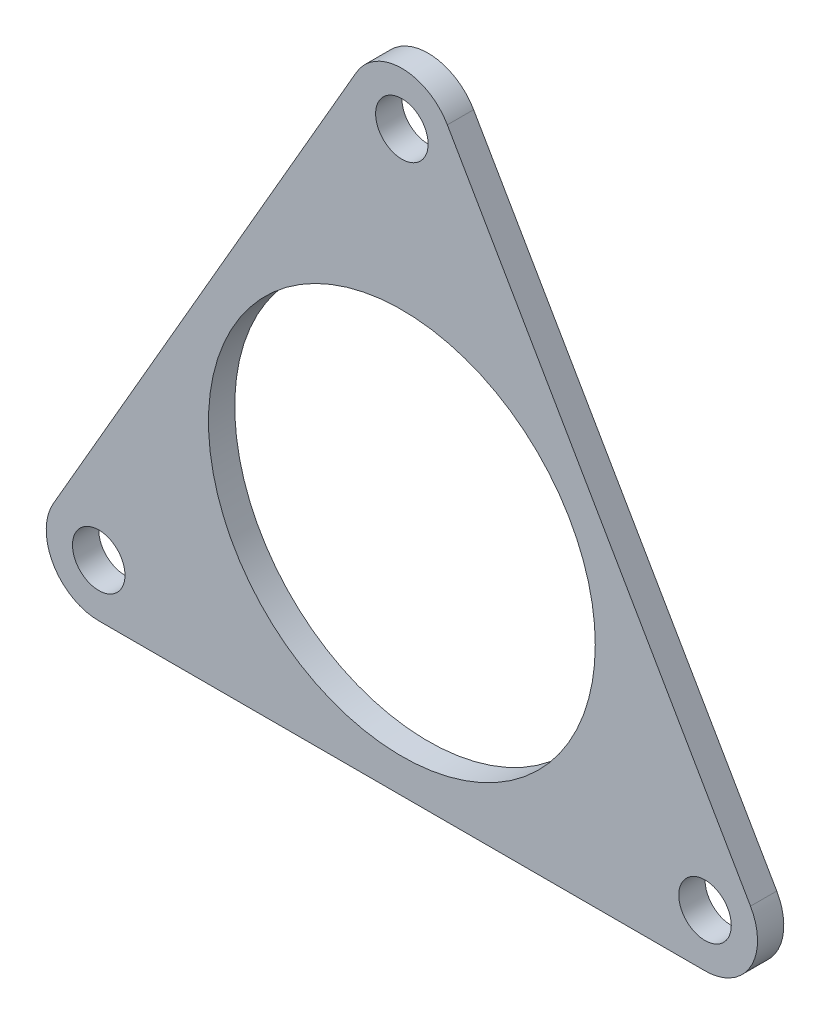
SolidWorks part; units mm, degrees
material "Thornel Mat VMA"
ref_plane "前视基准面" through (0, 0, 0) normal (0, 0, 1) x (1, 0, 0)
ref_plane "上视基准面" through (0, 0, 0) normal (0, 1, 0) x (1, 0, 0)
ref_plane "右视基准面" through (0, 0, 0) normal (1, 0, 0) x (0, 0, -1)
sketch "草图1" plane through (0, 0, 0) normal (0, 0, 1) x (1, 0, 0)
  line L0 (0, 20) -> (-17.3205, -10) construction
  line L1 (-17.3205, -10) -> (17.3205, -10) construction
  line L2 (17.3205, -10) -> (0, 20) construction
  line L3 (-2.5981, 21.5) -> (-19.9186, -8.5)
  line L4 (-17.3205, -13) -> (17.3205, -13)
  line L5 (19.9186, -8.5) -> (2.5981, 21.5)
  circle A0 centre (0, 0) radius 20 construction
  circle A1 centre (-17.3205, -10) radius 1.5
  circle A2 centre (0, 20) radius 1.5
  circle A3 centre (17.3205, -10) radius 1.5
  circle A4 centre (0, 0) radius 5 construction
  circle A5 centre (0, 0) radius 7 construction
  circle A6 centre (0, 7) radius 1.5 construction
  circle A7 centre (0, -7) radius 1.5 construction
  circle A8 centre (0, 0) radius 26 construction
  arc A9 (-19.9186, -8.5) -> (-17.3205, -13) centre (-17.3205, -10) ccw
  arc A10 (17.3205, -13) -> (19.9186, -8.5) centre (17.3205, -10) ccw
  arc A11 (-2.5981, 21.5) -> (2.5981, 21.5) centre (0, 20) cw
  circle A12 centre (0, 0) radius 11.05
  point P23 (-22.5167, -13)
  point P26 (22.5167, -13)
  point P29 (0, 26)
  dimension "D1" = 40
  dimension "D2" = 3
  dimension "D3" = 10
  dimension "D4" = 14
  dimension "D5" = 3
  dimension "D6" = 3
  dimension "D7" = 3
  dimension "D8" = 22.1
extrude "凸台-拉伸1" add sketch "草图1" along normal blind 1.5
